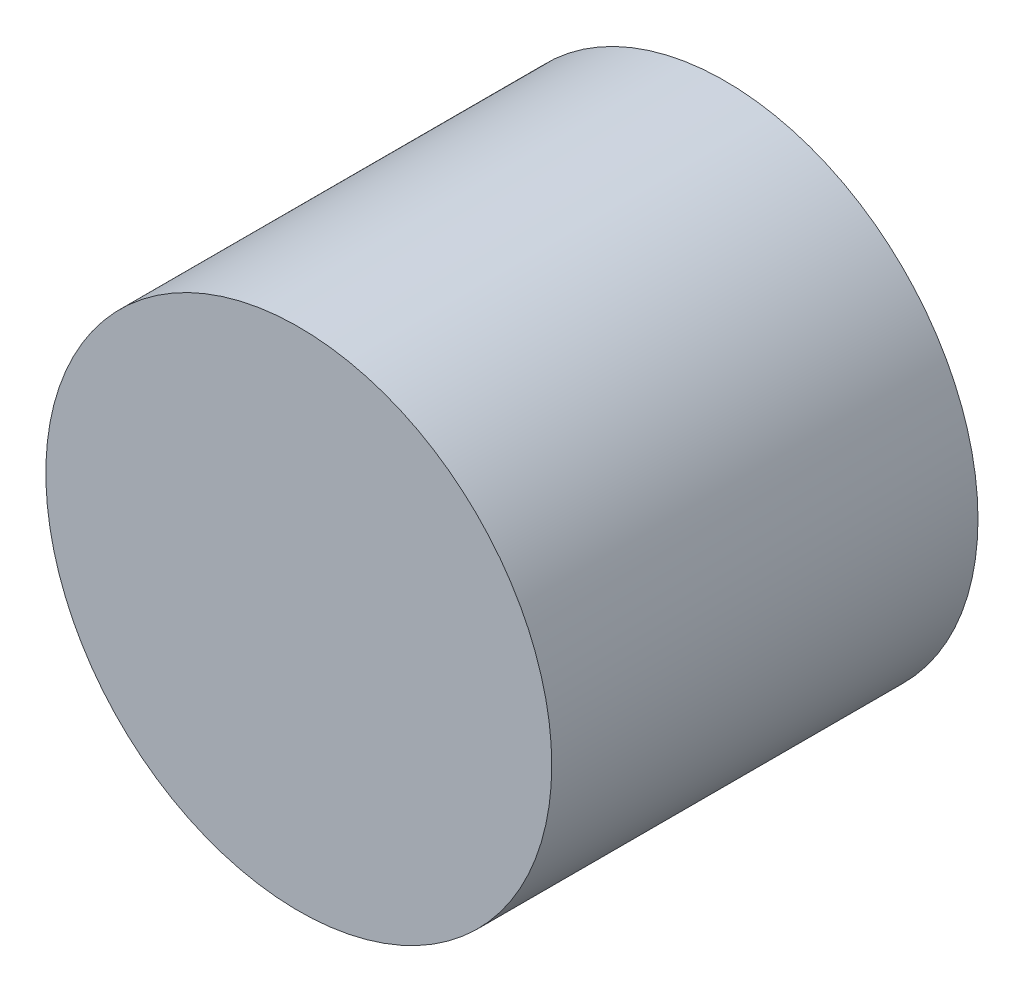
SolidWorks part; units mm, degrees
ref_plane "Plan de face" through (0, 0, 0) normal (0, 0, 1) x (1, 0, 0)
ref_plane "Plan de dessus" through (0, 0, 0) normal (0, 1, 0) x (1, 0, 0)
ref_plane "Plan de droite" through (0, 0, 0) normal (1, 0, 0) x (0, 0, -1)
sketch "Sketch1" plane through (0, 0, 0) normal (0, 0, 1) x (1, 0, 0)
  circle A0 centre (0, 0) radius 63.5
  dimension "D1" = 127
extrude "Boss-Extrude1" add sketch "Sketch1" along normal blind 107
